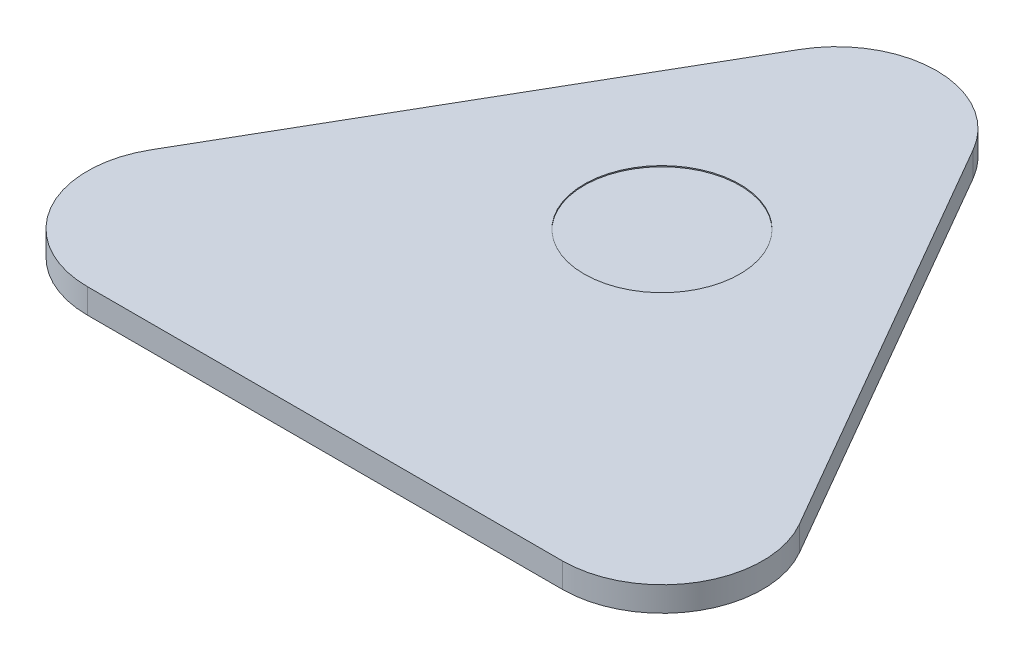
SolidWorks part; units mm, degrees
ref_plane "Front Plane" through (0, 0, 0) normal (0, 0, 1) x (1, 0, 0)
ref_plane "Top Plane" through (0, 0, 0) normal (0, 1, 0) x (1, 0, 0)
ref_plane "Right Plane" through (0, 0, 0) normal (1, 0, 0) x (0, 0, -1)
sketch "Sketch1" plane through (0, 0, 0) normal (0, 1, 0) x (1, 0, 0)
  line L0 (-8.3571, 31.2388) -> (-31.2321, -8.3819)
  line L1 (-5.7591, 29.7388) -> (-28.6341, -9.8819) construction
  line L2 (-22.875, -19.8569) -> (22.875, -19.8569) construction
  line L3 (28.6341, -9.8819) -> (5.7591, 29.7388) construction
  line L4 (-22.875, -22.8569) -> (22.875, -22.8569)
  line L5 (31.2321, -8.3819) -> (8.3571, 31.2388)
  circle A0 centre (0, 0) radius 19.8569 construction
  arc A1 (-28.6341, -9.8819) -> (-22.875, -19.8569) centre (-22.875, -13.2069) ccw construction
  arc A2 (22.875, -19.8569) -> (28.6341, -9.8819) centre (22.875, -13.2069) ccw construction
  arc A3 (-5.7591, 29.7388) -> (5.7591, 29.7388) centre (0, 26.4138) cw construction
  arc A4 (-31.2321, -8.3819) -> (-22.875, -22.8569) centre (-22.875, -13.2069) ccw
  arc A5 (22.875, -22.8569) -> (31.2321, -8.3819) centre (22.875, -13.2069) ccw
  arc A6 (-8.3571, 31.2388) -> (8.3571, 31.2388) centre (0, 26.4138) cw
  point P6 (-34.3931, -19.8569)
  point P11 (34.3931, -19.8569)
  dimension "D2" = 6.65
  dimension "D1" = 45.75
  dimension "D3" = 3
extrude "Boss-Extrude1" add sketch "Sketch1" along normal blind 2.3813
sketch "Sketch2" plane through (0, 2.3813, 0) normal (0, 1, 0) x (1, 0, 0)
  circle A0 centre (0, 9.6138) radius 7.5
  arc A1 (8.3571, 31.2388) -> (-8.3571, 31.2388) centre (0, 26.4138) ccw construction
  point P5 (0, 0)
  dimension "D1" = 16.8
  dimension "D2" = 15
extrude "Cut-Extrude1" cut sketch "Sketch2" against normal blind 0.1
